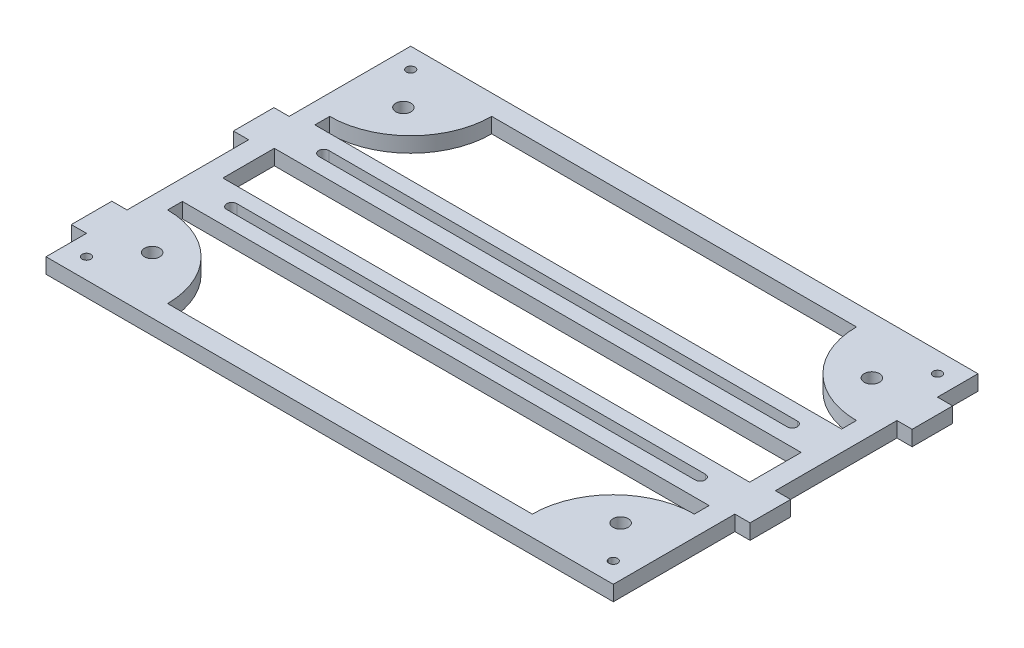
SolidWorks part; units mm, degrees
material "6061-T6 (SS)"
ref_plane "Front Plane" through (0, 0, 0) normal (0, 0, 1) x (1, 0, 0)
ref_plane "Top Plane" through (0, 0, 0) normal (0, 1, 0) x (1, 0, 0)
ref_plane "Right Plane" through (0, 0, 0) normal (1, 0, 0) x (0, 0, -1)
sketch "Sketch1" plane through (0, 0, 0) normal (0, 1, 0) x (1, 0, 0)
  line L0 (-82.55, -25.4) -> (-82.55, -20.7675)
  line L1 (88.9, -57.15) -> (-88.9, -57.15)
  line L2 (88.9, -57.15) -> (88.9, 57.15)
  line L3 (88.9, 57.15) -> (-88.9, 57.15)
  line L4 (-88.9, -57.15) -> (-88.9, 57.15)
  line L5 (88.9, -57.15) -> (-88.9, 57.15) construction
  line L6 (88.9, 57.15) -> (-88.9, -57.15) construction
  line L7 (57.15, -50.8) -> (-57.15, -50.8)
  line L8 (82.55, -25.4) -> (82.55, -20.7675)
  line L10 (82.55, -20.7675) -> (-82.55, -20.7675)
  line L11 (82.55, -8.0675) -> (-82.55, -8.0675)
  line L12 (0, 0) -> (-76.2, 0) construction
  line L13 (82.55, 8.0675) -> (-82.55, 8.0675)
  line L14 (82.55, 20.7675) -> (-82.55, 20.7675)
  line L15 (-82.55, -8.0675) -> (-82.55, 8.0675)
  line L16 (-82.55, -50.8) -> (-82.55, 50.8) construction
  line L17 (82.55, -8.0675) -> (82.55, 8.0675)
  line L18 (82.55, -50.8) -> (82.55, 50.8) construction
  line L19 (-82.55, 20.7675) -> (-82.55, 25.4)
  line L20 (82.55, 20.7675) -> (82.55, 25.4)
  line L21 (0, 0) -> (0, 34.6317) construction
  line L22 (82.55, 50.8) -> (-82.55, 50.8) construction
  line L23 (82.55, -50.8) -> (-82.55, -50.8) construction
  line L24 (57.15, 50.8) -> (-57.15, 50.8)
  arc A0 (-57.15, -50.8) -> (-82.55, -25.4) centre (-82.55, -50.8) ccw
  arc A1 (57.15, -50.8) -> (82.55, -25.4) centre (82.55, -50.8) cw
  arc A2 (57.15, 50.8) -> (82.55, 25.4) centre (82.55, 50.8) ccw
  arc A3 (-57.15, 50.8) -> (-82.55, 25.4) centre (-82.55, 50.8) cw
  point P0 (0, 0)
  dimension "D6" = 6.35
  dimension "D4" = 25.4
  dimension "D1" = 114.3
  dimension "D2" = 177.8
  dimension "D5" = 12.7
  dimension "D3" = 6.35
extrude "Boss-Extrude1" add sketch "Sketch1" along normal blind 4.7625
sketch "Sketch3" plane through (0, 4.7625, 0) normal (0, 1, 0) x (1, 0, 0)
  line L0 (-73.406, 14.4175) -> (73.406, 14.4175) construction
  line L1 (-73.406, 16.005) -> (73.406, 16.005)
  line L2 (-73.406, 12.83) -> (73.406, 12.83)
  line L3 (82.55, 20.7675) -> (-82.55, 20.7675) construction
  line L6 (82.55, 8.0675) -> (-82.55, 8.0675) construction
  line L7 (0, 0) -> (40.1052, 0) construction
  line L8 (-73.406, -14.4175) -> (73.406, -14.4175) construction
  line L9 (-73.406, -16.005) -> (73.406, -16.005)
  line L10 (-73.406, -12.83) -> (73.406, -12.83)
  arc A0 (-73.406, 16.005) -> (-73.406, 12.83) centre (-73.406, 14.4175) ccw
  arc A1 (73.406, 12.83) -> (73.406, 16.005) centre (73.406, 14.4175) ccw
  arc A2 (-73.406, -16.005) -> (-73.406, -12.83) centre (-73.406, -14.4175) cw
  arc A3 (73.406, -12.83) -> (73.406, -16.005) centre (73.406, -14.4175) cw
  point P2 (0, 14.4175)
  point P11 (0, 8.0675)
  point P17 (0, -14.4175)
  dimension "D1" = 1.5875
  dimension "D2" = 6.35
  dimension "D3" = 146.812
extrude "Cut-Extrude1" cut sketch "Sketch3" against normal through all
sketch "Sketch4" plane through (0, 4.7625, 0) normal (0, 1, 0) x (1, 0, 0)
  line L0 (88.9, 57.15) -> (-88.9, 57.15) construction
  line L2 (0, 0) -> (0, 32.076) construction
  line L3 (0, 0) -> (41.2704, 0) construction
  circle A0 centre (-73.406, 39.37) radius 2.3813
  circle A1 centre (-73.406, -39.37) radius 2.3813
  circle A2 centre (73.406, -39.37) radius 2.3813
  circle A3 centre (73.406, 39.37) radius 2.3813
  arc A4 (-73.406, 16.005) -> (-73.406, 12.83) centre (-73.406, 14.4175) ccw construction
  arc A5 (-73.406, 16.005) -> (-73.406, 12.83) centre (-73.406, 14.4175) ccw
  dimension "D1" = 4.7625
  dimension "D2" = 17.78
extrude "Cut-Extrude2" cut sketch "Sketch4" against normal through all contours A1 | A0 | A3 | A2
hole_wizard "#6-32 Tapped Hole1" positions "Sketch5" profile "Sketch6" tap size "#6-32" standard "Ansi Inch" end condition through all
sketch "Sketch5" plane through (0, 6.2865, 0) normal (0, 1, 0) x (-1, 0, 0)
  line L2 (0, 0) -> (0, 35.5851) construction
  line L4 (0, 0) -> (43.0458, 0) construction
  point P0 (82.55, -50.8)
  point P15 (82.55, 50.8)
  point P16 (-82.55, 50.8)
  point P17 (-82.55, -50.8)
sketch "Sketch6" plane through (-82.55, 6.2865, -50.8) normal (1, 0, 0) x (0, 0, 1)
  line L0 (0, 0) -> (0, 6.2865)
  line L1 (0, 6.2865) -> (1.3525, 6.2865)
  line L2 (1.3525, 6.2865) -> (1.3525, 0)
  line L3 (1.3525, 0) -> (0, 0)
  line L4 (0, -6.35) -> (0, 107.95) construction
  dimension "Thru Tap Drill Dia." = 2.7051
  dimension "Thru Tap Drill Depth" = 6.2865
cosmetic thread "Hole Thread1" parameters "D1"=6.2865, "D2"=3.5052
cosmetic thread "Hole Thread2" parameters "D1"=6.2865, "D2"=3.5052
cosmetic thread "Hole Thread3" parameters "D1"=6.2865, "D2"=3.5052
cosmetic thread "Hole Thread4" parameters "D1"=6.2865, "D2"=3.5052
sketch "Sketch7" plane through (-88.9, 0, 0) normal (-1, 0, 0) x (0, 0, 1)
  line L0 (-57.15, 2.3813) -> (57.15, 2.3813) construction
  line L1 (-57.15, 4.7625) -> (-57.15, 0) construction
  line L2 (57.15, 4.7625) -> (57.15, 0) construction
  line L4 (-6.35, 4.7625) -> (-19.05, 4.7625)
  line L5 (-6.35, 4.7625) -> (-6.35, 0)
  line L6 (-6.35, 0) -> (-19.05, 0)
  line L7 (-19.05, 4.7625) -> (-19.05, 0)
  line L8 (-6.35, 4.7625) -> (-19.05, 0) construction
  line L9 (-6.35, 0) -> (-19.05, 4.7625) construction
  line L10 (44.45, 4.7625) -> (31.75, 4.7625)
  line L11 (44.45, 4.7625) -> (44.45, 0)
  line L12 (44.45, 0) -> (31.75, 0)
  line L13 (31.75, 4.7625) -> (31.75, 0)
  line L14 (44.45, 4.7625) -> (31.75, 0) construction
  line L15 (44.45, 0) -> (31.75, 4.7625) construction
  point P6 (-12.7, 2.3813)
  point P11 (38.1, 2.3813)
  dimension "D1" = 12.7
  dimension "D2" = 12.7
  dimension "D3" = 4.7625
  dimension "D4" = 4.7625
  dimension "D5" = 19.05
  dimension "D6" = 50.8
extrude "Boss-Extrude2" add sketch "Sketch7" along normal blind 4.7625
sketch "Sketch8" plane through (88.9, 0, 0) normal (1, 0, 0) x (0, 0, -1)
  line L0 (-57.15, 2.3813) -> (57.15, 2.3813) construction
  line L1 (-57.15, 4.7625) -> (-57.15, 0) construction
  line L2 (57.15, 4.7625) -> (57.15, 0) construction
  line L4 (-6.35, 4.7625) -> (-19.05, 4.7625)
  line L5 (-6.35, 4.7625) -> (-6.35, 0)
  line L6 (-6.35, 0) -> (-19.05, 0)
  line L7 (-19.05, 4.7625) -> (-19.05, 0)
  line L8 (-6.35, 4.7625) -> (-19.05, 0) construction
  line L9 (-6.35, 0) -> (-19.05, 4.7625) construction
  line L10 (44.45, 4.7625) -> (31.75, 4.7625)
  line L11 (44.45, 4.7625) -> (44.45, 0)
  line L12 (44.45, 0) -> (31.75, 0)
  line L13 (31.75, 4.7625) -> (31.75, 0)
  line L14 (44.45, 4.7625) -> (31.75, 0) construction
  line L15 (44.45, 0) -> (31.75, 4.7625) construction
  point P6 (-12.7, 2.3813)
  point P11 (38.1, 2.3813)
  dimension "D1" = 12.7
  dimension "D2" = 4.7625
  dimension "D3" = 19.05
  dimension "D4" = 12.7
  dimension "D5" = 4.7625
  dimension "D6" = 50.8
extrude "Boss-Extrude3" add sketch "Sketch8" along normal blind 4.7625
equation "\"D2@Sketch3\" = \"D5@Sketch1\"/2"
